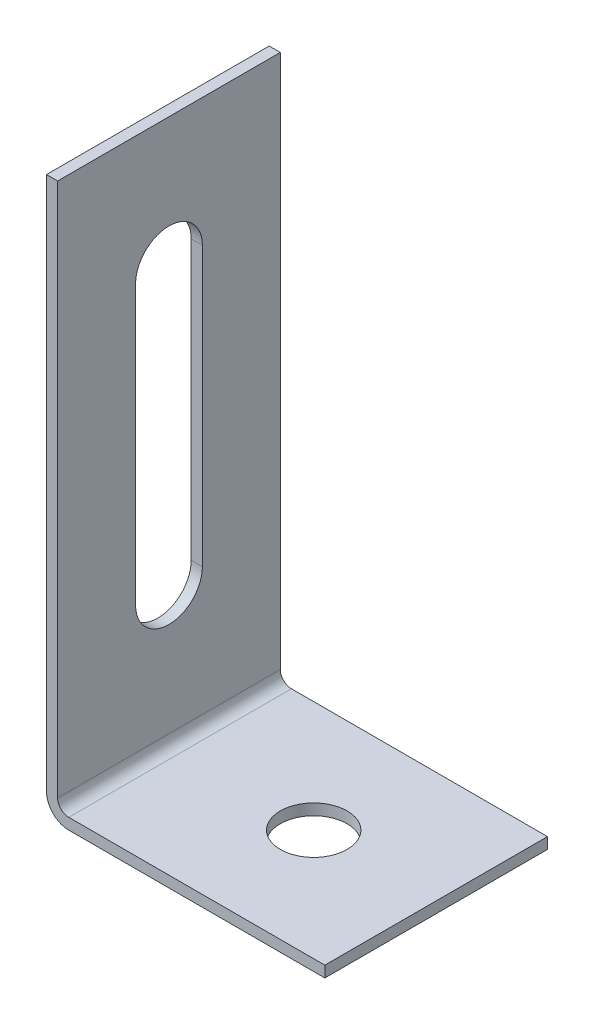
SolidWorks part; units mm, degrees
material "6061 Alloy"
ref_plane "Front Plane" through (0, 0, 0) normal (0, 0, 1) x (1, 0, 0)
ref_plane "Top Plane" through (0, 0, 0) normal (0, 1, 0) x (1, 0, 0)
ref_plane "Right Plane" through (0, 0, 0) normal (1, 0, 0) x (0, 0, -1)
sketch "Sketch2" plane through (0, 0, 0) normal (0, 0, 1) x (1, 0, 0)
  line L0 (0, 2) -> (0, 50)
  line L1 (2, 0) -> (25, 0)
  line L2 (2, 1) -> (25, 1)
  line L3 (1, 2) -> (1, 50)
  line L4 (0, 50) -> (1, 50)
  line L5 (25, 1) -> (25, 0)
  line L6 (0, 0) -> (0, 50) construction
  line L7 (0, 0) -> (25, 0) construction
  line L8 (1, 1) -> (25, 1) construction
  line L9 (1, 1) -> (1, 50) construction
  arc A0 (0, 2) -> (2, 0) centre (2, 2) ccw
  arc A1 (2, 1) -> (1, 2) centre (2, 2) cw
  dimension "D1" = 2
  dimension "D2" = 50
  dimension "D7" = 1
  dimension "D4" = 2
  dimension "D5" = 2
  dimension "D6" = 25
  dimension "D3" = 1
extrude "Boss-Extrude1" add sketch "Sketch2" along normal blind 20
sketch "Sketch3" plane through (1, 0, 0) normal (1, 0, 0) x (0, 0, -1)
  line L0 (-10, 50) -> (-10, 2) construction
  line L1 (-20, 50) -> (0, 50) construction
  line L2 (-20, 2) -> (0, 2) construction
  line L3 (-10, 13.5) -> (-10, 38.5) construction
  line L5 (-13, 13.5) -> (-13, 38.5)
  line L6 (-7, 13.5) -> (-7, 38.5)
  arc A0 (-13, 13.5) -> (-7, 13.5) centre (-10, 13.5) ccw
  arc A1 (-7, 38.5) -> (-13, 38.5) centre (-10, 38.5) ccw
  point P10 (-10, 26)
  dimension "D1" = 3
  dimension "D2" = 25
extrude "Cut-Extrude1" cut sketch "Sketch3" against normal blind 10
sketch "Sketch4" plane through (0, 1, 0) normal (0, 1, 0) x (1, 0, 0)
  line L0 (25, -10) -> (2, -10) construction
  line L1 (25, -20) -> (25, 0) construction
  line L2 (2, -20) -> (2, 0) construction
  circle A0 centre (14, -10) radius 3
  dimension "D1" = 6
  dimension "D2" = 12
extrude "Cut-Extrude2" cut sketch "Sketch4" against normal blind 10
